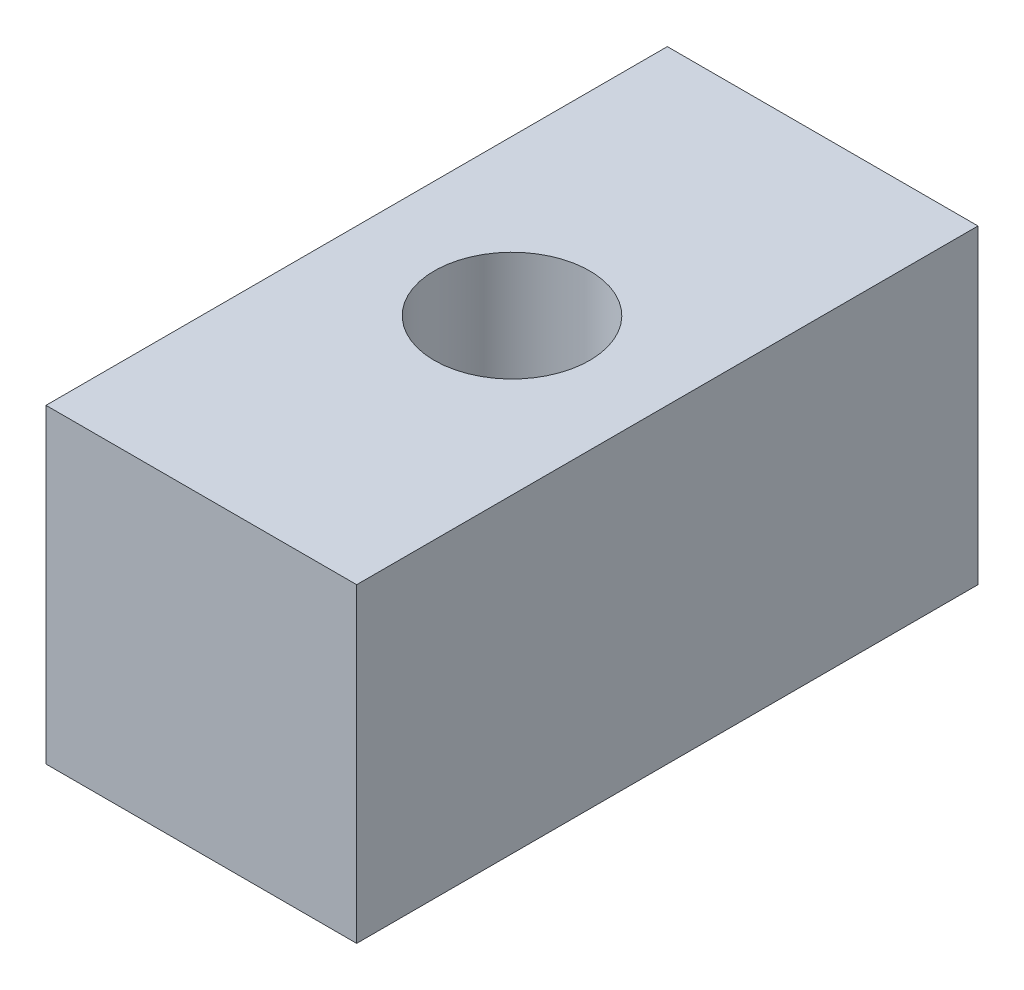
SolidWorks part; units mm, degrees
ref_plane "Front" through (0, 0, 0) normal (0, 0, 1) x (1, 0, 0)
ref_plane "Top" through (0, 0, 0) normal (0, 1, 0) x (1, 0, 0)
ref_plane "Right" through (0, 0, 0) normal (1, 0, 0) x (0, 0, -1)
sketch "Sketch1" plane through (0, 0, 0) normal (0, 1, 0) x (1, 0, 0)
  line L1 (12.7, -25.4) -> (-12.7, -25.4)
  line L2 (12.7, -25.4) -> (12.7, 25.4)
  line L3 (12.7, 25.4) -> (-12.7, 25.4)
  line L4 (-12.7, -25.4) -> (-12.7, 25.4)
  line L5 (12.7, -25.4) -> (-12.7, 25.4) construction
  line L6 (12.7, 25.4) -> (-12.7, -25.4) construction
  point P0 (0, 0)
  dimension "D1" = 25.4
  dimension "D2" = 50.8
extrude "Boss-Extrude1" add sketch "Sketch1" along normal blind 25.4
sketch "Sketch2" plane through (0, 25.4, 0) normal (0, 1, 0) x (1, 0, 0)
  circle A0 centre (0, 0) radius 6.35
  dimension "D1" = 12.7
extrude "Cut-Extrude1" cut sketch "Sketch2" against normal up to next
